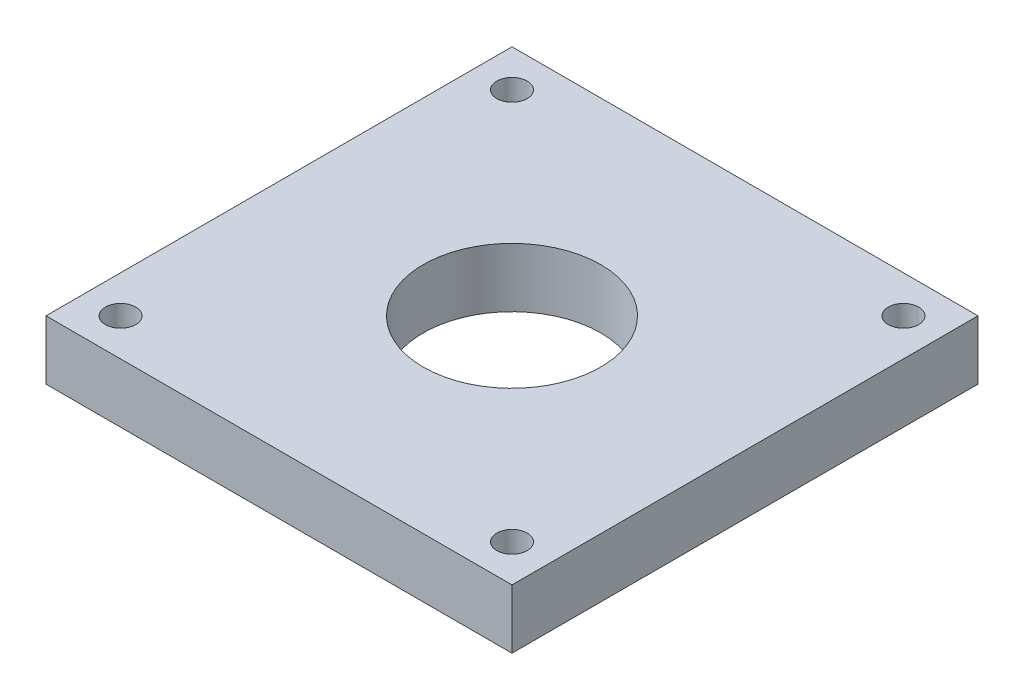
SolidWorks part; units mm, degrees
ref_plane "Front Plane" through (0, 0, 0) normal (0, 0, 1) x (1, 0, 0)
ref_plane "Top Plane" through (0, 0, 0) normal (0, 1, 0) x (1, 0, 0)
ref_plane "Right Plane" through (0, 0, 0) normal (1, 0, 0) x (0, 0, -1)
sketch "Sketch2" plane through (0, 0, 0) normal (0, 1, 0) x (1, 0, 0)
  line L0 (-25, 25) -> (25, 25)
  line L1 (-25, 25) -> (-25, -25)
  line L2 (-25, -25) -> (25, -25)
  line L3 (25, 25) -> (25, -25)
  line L4 (-25, -25) -> (25, 25) construction
  circle A0 centre (0, 0) radius 9.525
  dimension "D1" = 19.05
  dimension "D2" = 50
extrude "Boss-Extrude1" add sketch "Sketch2" along normal blind 6.35
hole_wizard "#4 Clearance Hole1" positions "Sketch4" profile "Sketch3" hole size "#4" standard "ANSI Inch" end condition through all
sketch "Sketch4" plane through (0, 6.35, 0) normal (0, 1, 0) x (1, 0, 0)
  line L0 (-21, -21) -> (21, 21) construction
  line L1 (21, 21) -> (21, -21) construction
  line L2 (21, -21) -> (-21, 21) construction
  line L3 (-21, 21) -> (-21, -21) construction
  line L5 (-21, -21) -> (21, -21) construction
  line L7 (-21, 21) -> (21, 21) construction
  line L9 (-25, 25) -> (-25, -25) construction
  line L10 (25, 25) -> (-25, 25) construction
  point P0 (-21, -21)
  point P2 (21, -21)
  point P4 (21, 21)
  point P6 (-21, 21)
  dimension "D1" = 4
  dimension "D2" = 4
sketch "Sketch3" plane through (-21, 6.35, 21) normal (1, 0, 0) x (0, 0, 1)
  line L0 (0, 0) -> (0, 6.35)
  line L1 (0, 6.35) -> (1.6319, 6.35)
  line L2 (1.6319, 6.35) -> (1.6319, 0)
  line L5 (1.6319, 0) -> (0, 0)
  line L11 (0, -6.35) -> (0, 107.95) construction
  dimension "Thru Hole Dia." = 3.2639
  dimension "Thru Hole Depth" = 6.35
